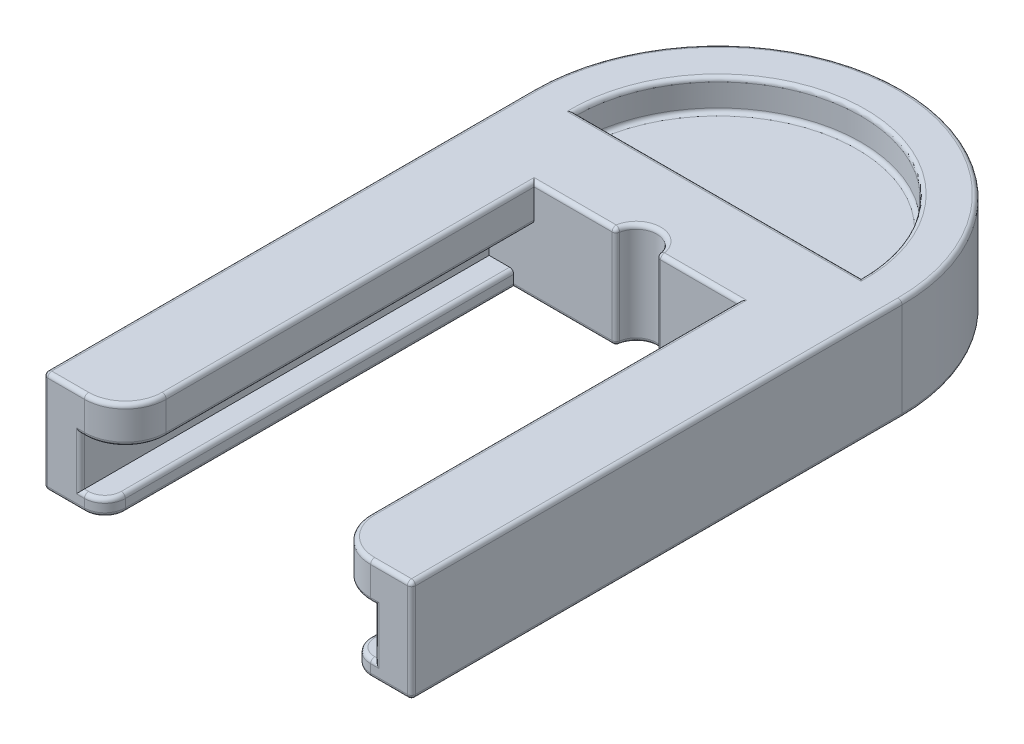
SolidWorks part; units mm, degrees
ref_plane "Front Plane" through (0, 0, 0) normal (0, 0, 1) x (1, 0, 0)
ref_plane "Top Plane" through (0, 0, 0) normal (0, 1, 0) x (1, 0, 0)
ref_plane "Right Plane" through (0, 0, 0) normal (1, 0, 0) x (0, 0, -1)
sketch "Sketch1" plane through (0, 0, 0) normal (0, 0, 1) x (1, 0, 0)
  line L0 (-17.5, 0) -> (17.5, 0) construction
  line L1 (-17.5, 2.5) -> (-17.5, -2.5) construction
  line L2 (-17.5, 2.5) -> (-12.5, 2.5) construction
  line L3 (-12.5, 2.5) -> (-12.5, 7.5) construction
  line L4 (-12.5, 7.5) -> (-22.5, 7.5)
  line L5 (-22.5, 7.5) -> (-22.5, -5)
  line L6 (-22.5, -5) -> (-15, -5)
  line L7 (-15, -5) -> (-15, -2.5) construction
  line L8 (-15, -2.5) -> (-17.5, -2.5) construction
  line L9 (0, 0) -> (0, 5.0668) construction
  line L10 (22.5, 7.5) -> (22.5, -5)
  line L11 (22.5, -5) -> (15, -5)
  line L12 (15, -5) -> (15, -2.5) construction
  line L13 (15, -2.5) -> (17.5, -2.5) construction
  line L14 (17.5, 2.5) -> (17.5, -2.5) construction
  line L15 (17.5, 2.5) -> (12.5, 2.5) construction
  line L16 (12.5, 2.5) -> (12.5, 7.5) construction
  line L17 (12.5, 7.5) -> (22.5, 7.5)
  line L18 (-15, -3) -> (-18, -3)
  line L19 (-18, 3) -> (-18, -3)
  line L20 (-18, 3) -> (-12.5, 3)
  line L21 (18, 3) -> (12.5, 3)
  line L22 (18, 3) -> (18, -3)
  line L23 (15, -3) -> (18, -3)
  line L24 (-12.5, 3) -> (-12.5, 7.5)
  line L25 (-15, -3) -> (-15, -5)
  line L26 (15, -3) -> (15, -5)
  line L27 (12.5, 3) -> (12.5, 7.5)
  point P3 (0, 0)
  point P6 (-17.5, 0)
  dimension "D1" = 35
  dimension "D2" = 2.5
  dimension "D3" = 2.5
  dimension "D4" = 5
  dimension "D5" = 5
  dimension "D7" = 5
  dimension "D6" = 5
  dimension "D8" = 0.5
extrude "Boss-Extrude1" add sketch "Sketch1" along normal blind 50
sketch "Sketch2" plane through (0, 0, 0) normal (0, 0, 1) x (1, 0, 0)
  line L0 (22.5, 7.5) -> (22.5, -5)
  line L1 (22.5, 7.5) -> (-22.5, 7.5)
  line L2 (22.5, -5) -> (-22.5, -5)
  line L3 (-22.5, 7.5) -> (-22.5, -5)
  line L4 (-22.5, 7.5) -> (-22.5, -5) construction
extrude "Boss-Extrude2" add sketch "Sketch2" against normal blind 10
ref_plane "Plane1" through (0, 1.25, 0) normal (0, 1, 0) x (1, 0, 0)
sketch "Sketch3" plane through (0, 1.25, 0) normal (0, -1, 0) x (1, 0, 0)
  line L3 (-22.5, -10) -> (22.5, -10) construction
  line L4 (-22.5, -10) -> (-17.5, -10)
  line L5 (17.5, -10) -> (22.5, -10)
  arc A2 (-22.5, -10) -> (22.5, -10) centre (0, -10) ccw
  arc A3 (-17.5, -10) -> (17.5, -10) centre (0, -10) ccw
  dimension "D1" = 5
extrude "Boss-Extrude3" add sketch "Sketch3" along normal up to surface and the other way up to surface
sketch "Sketch4" plane through (0, 1.25, 0) normal (0, 1, 0) x (1, 0, 0)
  line L1 (-17.5, 10) -> (17.5, 10) construction
  line L2 (-17.5, 10) -> (17.5, 10)
  arc A2 (17.5, 10) -> (-17.5, 10) centre (0, 10) ccw construction
  arc A3 (17.5, 10) -> (-17.5, 10) centre (0, 10) ccw
extrude "Boss-Extrude4" add sketch "Sketch4" along normal blind 2.5 and the other way blind 2.5
fillet "Fillet1" radius 5 2 edges at (12.5, 5.25, 50) (-12.5, 5.25, 50)
fillet "Fillet2" radius 2.5 2 edges at (15, -4, 50) (-15, -4, 50)
sketch "Sketch5" plane through (0, 7.5, 0) normal (0, 1, 0) x (1, 0, 0)
  circle A0 centre (0, 0) radius 2.5
  dimension "D1" = 5
extrude "Cut-Extrude1" cut sketch "Sketch5" against normal through all
fillet "Fillet3" radius 0.5 50 edges at (0, -1.25, -10) (0, -1.25, -27.5) (0, 3.75, -10) (0, 3.75, -27.5) (0, 7.5, -27.5) (0, -5, -27.5) (0, -5, -10) (20, -5, 50) (22.5, -5, 20) (0, -5, -32.5) (0, 7.5, -32.5) (-22.5, -5, 20) (-20, -5, 50) (-8.75, -5, 0) (0, -5, -2.5) (8.75, -5, 0) (-20, 7.5, 50) (-22.5, 7.5, 20) (22.5, 7.5, 20) (20, 7.5, 50) (7.5, 7.5, 0) (0, 7.5, -2.5) (-7.5, 7.5, 0) (0, 7.5, -10) (-22.5, 1.25, 50) (22.5, 1.25, 50) (2.5, 1.25, 0) (-2.5, 1.25, 0) (15, -5, 23.75) (-15, -5, 23.75) (-12.5, 7.5, 22.5) (12.5, 7.5, 22.5) (-13.9645, 7.5, 48.5355) (13.9645, 7.5, 48.5355) (15.7322, -5, 49.2678) (-15.7322, -5, 49.2678) (17.75, -3, 50) (15.7322, -3, 49.2678) (17.75, 3, 50) (13.9645, 3, 48.5355) (-17.75, 3, 50) (-13.9645, 3, 48.5355) (-17.75, -3, 50) (-15.7322, -3, 49.2678) (18, 0, 50) (15, -3, 23.75) (12.5, 3, 22.5) (-12.5, 3, 22.5) (-18, 0, 50) (-15, -3, 23.75)
equation "\"SlideTolerance\"= .5mm"
equation "\"D8@Sketch1\"=\"SlideTolerance\""
